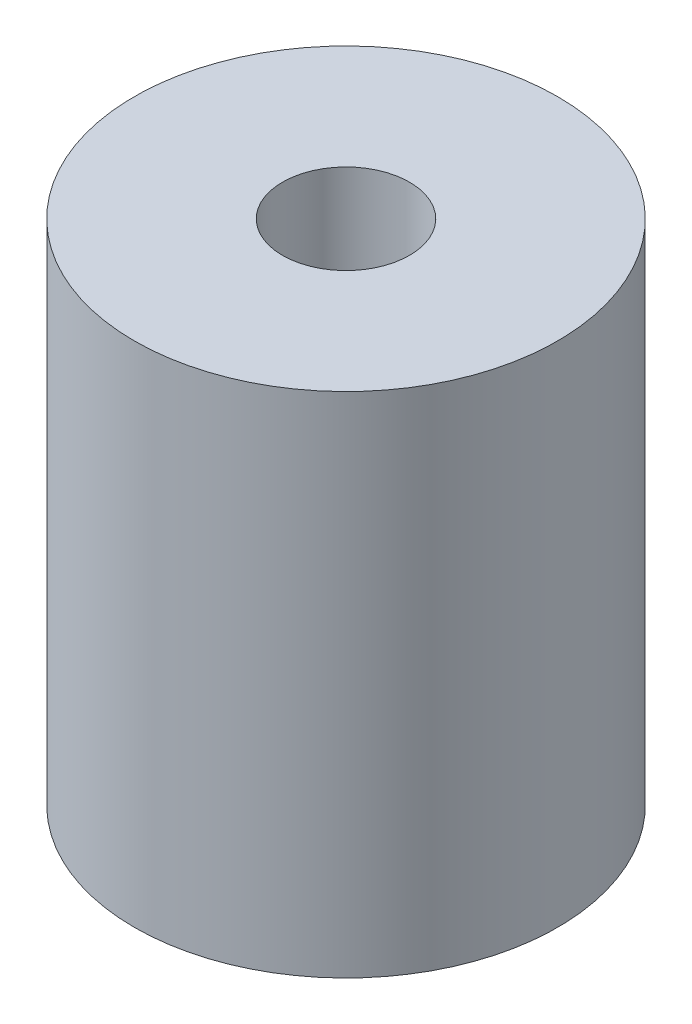
SolidWorks part; units mm, degrees
ref_plane "Alzado" through (0, 0, 0) normal (0, 0, 1) x (1, 0, 0)
ref_plane "Planta" through (0, 0, 0) normal (0, 1, 0) x (1, 0, 0)
ref_plane "Vista lateral" through (0, 0, 0) normal (1, 0, 0) x (0, 0, -1)
sketch "Croquis1" plane through (0, 0, 0) normal (0, 1, 0) x (1, 0, 0)
  circle A0 centre (0, 0) radius 5
  dimension "D1" = 10
extrude "Saliente-Extruir1" add sketch "Croquis1" along normal blind 12
sketch "Croquis2" plane through (0, 12, 0) normal (0, 1, 0) x (1, 0, 0)
  circle A0 centre (0, 0) radius 1.5
  dimension "D1" = 3
extrude "Cortar-Extruir1" cut sketch "Croquis2" against normal blind 5
sketch "Croquis4" plane through (0, 0, 0) normal (0, -1, 0) x (1, 0, 0)
  circle A0 centre (0, 0) radius 1.5
  dimension "D1" = 3
extrude "Cortar-Extruir2" cut sketch "Croquis4" against normal blind 5
